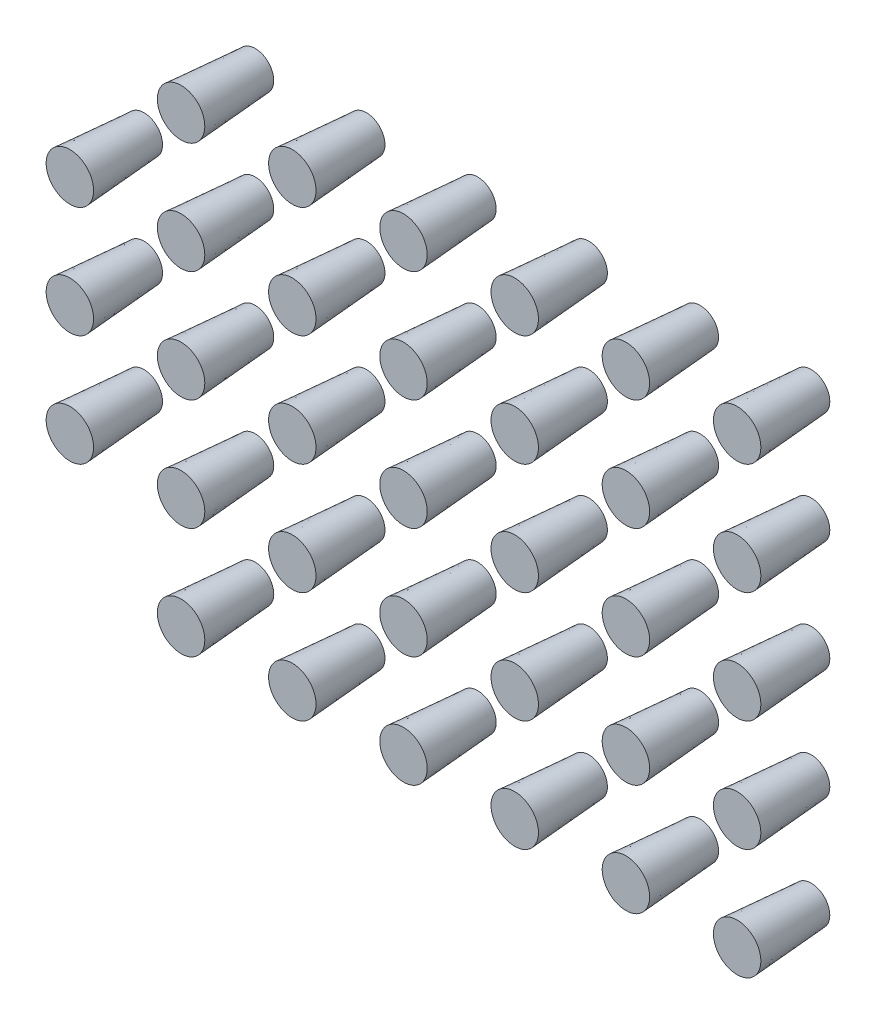
SolidWorks part; units mm, degrees
ref_plane "前视基准面" through (0, 0, 0) normal (0, 0, 1) x (1, 0, 0)
ref_plane "上视基准面" through (0, 0, 0) normal (0, 1, 0) x (1, 0, 0)
ref_plane "右视基准面" through (0, 0, 0) normal (1, 0, 0) x (0, 0, -1)
other "Configuration Table"
sketch "草图1" plane through (0, 0, 0) normal (0, 0, 1) x (1, 0, 0)
  circle A0 centre (0, 0) radius 0.5
  dimension "D1" = 1
extrude "凸台-拉伸1" add sketch "草图1" along normal blind 2 draft 4 draft outward yes
pattern_linear "阵列(线性)1" count 6 spacing 3 along (0, 1, 0) count 6 spacing 3 along (1, 0, 0) of "凸台-拉伸1"
ref_plane "基准面1" through (7.5, 0, 0) normal (1, 0, 0) x (0, 0, -1)
ref_plane "基准面2" through (0, 7.5, 0) normal (0, 1, 0) x (1, 0, 0)
pattern_linear "阵列(线性)2" count 2 spacing 3 along (-1, 0, 0) of bodies 110 109 108 107
pattern_linear "阵列(线性)3" count 2 spacing 3 along (-1, 0, 0) of bodies 143 144
delete or keep bodies "实体-删除/保留 1" type keep bodies bodies 144 121 138 115 132 109 126 143 120 137 114 131 108 125 119 136 113 130 107 124 118 112 106 140 134 128 145 122 139 116 133 110 127
